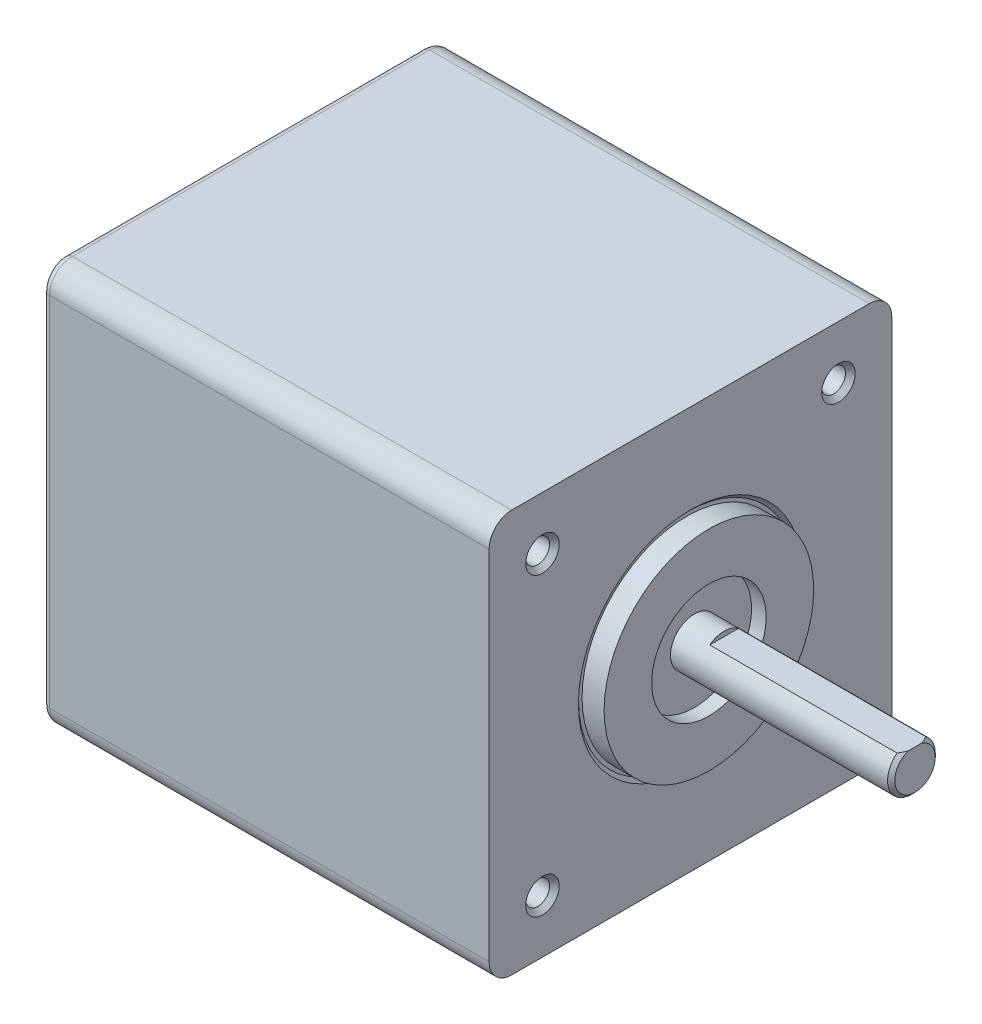
SolidWorks part; units mm, degrees
material "1023 Carbon Steel Sheet (SS)"
ref_plane "Front Plane" through (0, 0, 0) normal (0, 0, 1) x (1, 0, 0)
ref_plane "Top Plane" through (0, 0, 0) normal (0, 1, 0) x (1, 0, 0)
ref_plane "Right Plane" through (0, 0, 0) normal (1, 0, 0) x (0, 0, -1)
sketch "Sketch1" plane through (0, 0, 0) normal (1, 0, 0) x (0, 0, -1)
  line L1 (21.082, 21.082) -> (-21.082, 21.082)
  line L2 (21.082, 21.082) -> (21.082, -21.082)
  line L3 (21.082, -21.082) -> (-21.082, -21.082)
  line L4 (-21.082, 21.082) -> (-21.082, -21.082)
  line L5 (21.082, 21.082) -> (-21.082, -21.082) construction
  line L6 (21.082, -21.082) -> (-21.082, 21.082) construction
  point P0 (0, 0)
  dimension "D1" = 42.164
extrude "Boss-Extrude1" add sketch "Sketch1" against normal blind 46.7868
fillet "Fillet1" radius 2.3622 4 edges at (-23.3934, -21.082, -21.082) (-23.3934, 21.082, -21.082) (-23.3934, -21.082, 21.082) (-23.3934, 21.082, 21.082)
sketch "Sketch2" plane through (0, 0, 0) normal (1, 0, 0) x (0, 0, -1)
  circle A0 centre (0, 0) radius 10.975
  dimension "D1" = 21.95
extrude "Boss-Extrude2" add sketch "Sketch2" along normal blind 1.9304
sketch "Sketch10" plane through (0, 0, 0) normal (0, 0, 1) x (1, 0, 0)
  line L0 (0, 10.975) -> (-0.381, 10.975)
  line L1 (-0.381, 10.975) -> (-0.381, 11.356)
  line L2 (-0.381, 11.356) -> (0, 11.737)
  line L3 (0, 10.975) -> (0, 11.737)
  line L4 (0, 18.7198) -> (0, -18.7198) construction
  line L5 (0, 0) -> (9.6597, 0) construction
  dimension "D1" = 0.381
  dimension "D2" = 0.762
  dimension "D3" = 0.381
revolve "Cut-Revolve1" cut sketch "Sketch10" angle 360 about L5
sketch "Sketch3" plane through (1.9304, 0, 0) normal (1, 0, 0) x (0, 0, -1)
  circle A0 centre (0, 0) radius 2.5
  dimension "D1" = 5
extrude "Boss-Extrude3" add sketch "Sketch3" along normal blind 21.59
chamfer "Chamfer1" distance 0.381 angle 45 1 edges at (23.5204, 0, -2.5)
sketch "Sketch18" plane through (1.9304, 0, 0) normal (1, 0, 0) x (0, 0, -1)
  circle A0 centre (0, 0) radius 2.5 construction
  circle A1 centre (0, 0) radius 2.5
  circle A2 centre (0, 0) radius 5.9944
  dimension "D1" = 11.9888
extrude "Cut-Extrude8" cut sketch "Sketch18" against normal blind 1.524
ref_plane "Plane2" through (0, 2.0828, 0) normal (0, 1, 0) x (-1, 0, 0)
sketch "Sketch7" plane through (0, 2.0828, 0) normal (0, 1, 0) x (-1, 0, 0)
  line L0 (-23.1394, -2.5) -> (-23.1394, 2.5) construction
  line L1 (-37.1094, 6.35) -> (-9.1694, 6.35)
  line L2 (-37.1094, 6.35) -> (-37.1094, -6.35)
  line L3 (-37.1094, -6.35) -> (-9.1694, -6.35)
  line L4 (-9.1694, 6.35) -> (-9.1694, -6.35)
  line L5 (-37.1094, 6.35) -> (-9.1694, -6.35) construction
  line L6 (-37.1094, -6.35) -> (-9.1694, 6.35) construction
  line L8 (84.8106, 6.35) -> (56.8706, 6.35) construction
  line L9 (84.8106, 6.35) -> (84.8106, -6.35) construction
  line L10 (84.8106, -6.35) -> (56.8706, -6.35) construction
  line L11 (56.8706, 6.35) -> (56.8706, -6.35) construction
  line L12 (84.8106, 6.35) -> (56.8706, -6.35) construction
  line L13 (84.8106, -6.35) -> (56.8706, 6.35) construction
  point P0 (-23.1394, 0)
  point P7 (70.8406, 0)
  dimension "D1" = 13.97
  dimension "D2" = 12.7
extrude "Cut-Extrude3" [suppressed] cut sketch "Sketch7" along normal through all
ref_plane "Plane1" through (-5.08, 0, 0) normal (1, 0, 0) x (0, 0, -1)
sketch "Sketch5" plane through (-5.08, 0, 0) normal (1, 0, 0) x (0, 0, -1)
  line L1 (15.5, -15.5) -> (-15.5, -15.5) construction
  line L2 (15.5, -15.5) -> (15.5, 15.5) construction
  line L3 (15.5, 15.5) -> (-15.5, 15.5) construction
  line L4 (-15.5, -15.5) -> (-15.5, 15.5) construction
  line L5 (15.5, -15.5) -> (-15.5, 15.5) construction
  line L6 (15.5, 15.5) -> (-15.5, -15.5) construction
  circle A0 centre (-15.5, 15.5) radius 1.2446
  circle A1 centre (-15.5, -15.5) radius 1.2446
  circle A2 centre (15.5, -15.5) radius 1.2446
  circle A3 centre (15.5, 15.5) radius 1.2446
  point P0 (0, 0)
  dimension "D2" = 2.4892
  dimension "D1" = 31
extrude "Cut-Extrude1" cut sketch "Sketch5" against normal through all and the other way through all
cosmetic thread "Cosmetic Thread1" parameters "D2"=3
cosmetic thread "Cosmetic Thread2" parameters "D2"=3
cosmetic thread "Cosmetic Thread3" parameters "D2"=3
cosmetic thread "Cosmetic Thread4" parameters "D2"=3
sketch "Sketch6" plane through (-5.08, 0, 0) normal (1, 0, 0) x (0, 0, -1)
  line L0 (15.5, -15.5) -> (-15.5, 15.5) construction
  line L1 (-14.7483, 14.7483) -> (-26.032, 14.7483)
  line L2 (-14.7483, 14.7483) -> (-14.7483, 26.032)
  line L3 (-14.7483, 26.032) -> (-26.032, 26.032)
  line L4 (-26.032, 14.7483) -> (-26.032, 26.032)
  line L5 (-14.7483, 14.7483) -> (-26.032, 26.032) construction
  line L6 (-14.7483, 26.032) -> (-26.032, 14.7483) construction
  line L7 (14.7483, 14.7483) -> (26.032, 14.7483)
  line L8 (14.7483, 14.7483) -> (14.7483, 26.032)
  line L9 (14.7483, 26.032) -> (26.032, 26.032)
  line L10 (26.032, 14.7483) -> (26.032, 26.032)
  line L11 (14.7483, 14.7483) -> (26.032, 26.032) construction
  line L12 (14.7483, 26.032) -> (26.032, 14.7483) construction
  line L13 (14.7483, -14.7483) -> (26.032, -14.7483)
  line L14 (14.7483, -14.7483) -> (14.7483, -26.032)
  line L15 (14.7483, -26.032) -> (26.032, -26.032)
  line L16 (26.032, -14.7483) -> (26.032, -26.032)
  line L17 (14.7483, -14.7483) -> (26.032, -26.032) construction
  line L18 (14.7483, -26.032) -> (26.032, -14.7483) construction
  line L19 (15.5, 15.5) -> (-15.5, -15.5) construction
  line L21 (-14.7483, -14.7483) -> (-26.032, -14.7483)
  line L22 (-14.7483, -14.7483) -> (-14.7483, -26.032)
  line L23 (-14.7483, -26.032) -> (-26.032, -26.032)
  line L24 (-26.032, -14.7483) -> (-26.032, -26.032)
  line L25 (-14.7483, -14.7483) -> (-26.032, -26.032) construction
  line L26 (-14.7483, -26.032) -> (-26.032, -14.7483) construction
  arc A0 (-18.7198, 21.082) -> (-21.082, 18.7198) centre (-18.7198, 18.7198) ccw construction
  arc A1 (21.082, 18.7198) -> (18.7198, 21.082) centre (18.7198, 18.7198) ccw construction
  arc A2 (18.7198, -21.082) -> (21.082, -18.7198) centre (18.7198, -18.7198) ccw construction
  arc A3 (-21.082, -18.7198) -> (-18.7198, -21.082) centre (-18.7198, -18.7198) ccw construction
  point P0 (-20.3901, 20.3901)
  point P8 (20.3901, 20.3901)
  point P16 (20.3901, -20.3901)
  point P26 (-20.3901, -20.3901)
fillet "Fillet4" radius 0.762 8 edges at (-46.7868, 0, -21.082) (-46.7868, -21.082, 0) (-46.7868, 0, 21.082) (-46.7868, 21.082, 0) (-46.7868, 20.3901, -20.3901) (-46.7868, 20.3901, 20.3901) (-46.7868, -20.3901, -20.3901) (-46.7868, -20.3901, 20.3901)
chamfer "Chamfer3" distance 0.508 angle 45 8 edges at (0, -15.5, 16.7446) (0, -15.5, -14.2554) (0, 15.5, -14.2554) (0, 15.5, 16.7446) (-46.7868, -15.5, -16.7446) (-46.7868, -15.5, 14.2554) (-46.7868, 15.5, 14.2554) (-46.7868, 15.5, -16.7446)
sketch "Sketch15" plane through (0, 21.082, 0) normal (0, 1, 0) x (1, 0, 0)
  line L0 (-46.7868, -18.7198) -> (-46.7868, 18.7198) construction
  line L1 (-44.3738, -5.08) -> (-34.2138, -5.08)
  line L2 (-44.3738, -5.08) -> (-44.3738, 5.08)
  line L3 (-44.3738, 5.08) -> (-34.2138, 5.08)
  line L4 (-34.2138, -5.08) -> (-34.2138, 5.08)
  line L5 (-44.3738, -5.08) -> (-34.2138, 5.08) construction
  line L6 (-44.3738, 5.08) -> (-34.2138, -5.08) construction
  point P0 (-39.2938, 0)
  dimension "D1" = 10.16
  dimension "D2" = 7.493
extrude "Boss-Extrude6" [suppressed] add sketch "Sketch15" along normal blind 3.3782
sketch "Sketch16" [suppressed] plane through (0, 24.4602, 0) normal (0, 1, 0) x (1, 0, 0)
  line L0 (-44.3738, 5.08) -> (-34.2138, -5.08) construction
  circle A0 centre (-39.2938, 0) radius 4.3818
extrude "Boss-Extrude7" [suppressed] add sketch "Sketch16" along normal blind 7.62
ref_plane "Plane3" through (0, 2, 0) normal (0, 1, 0) x (1, 0, 0)
sketch "Sketch19" plane through (0, 2, 0) normal (0, 1, 0) x (1, 0, 0)
  line L0 (23.5204, -2.119) -> (23.5204, 2.119) construction
  line L1 (43.5204, -13.6401) -> (3.5204, -13.6401)
  line L2 (43.5204, -13.6401) -> (43.5204, 13.6401)
  line L3 (43.5204, 13.6401) -> (3.5204, 13.6401)
  line L4 (3.5204, -13.6401) -> (3.5204, 13.6401)
  line L5 (43.5204, -13.6401) -> (3.5204, 13.6401) construction
  line L6 (43.5204, 13.6401) -> (3.5204, -13.6401) construction
  point P0 (23.5204, 0)
  dimension "D1" = 20
extrude "Cut-Extrude9" cut sketch "Sketch19" along normal through all
